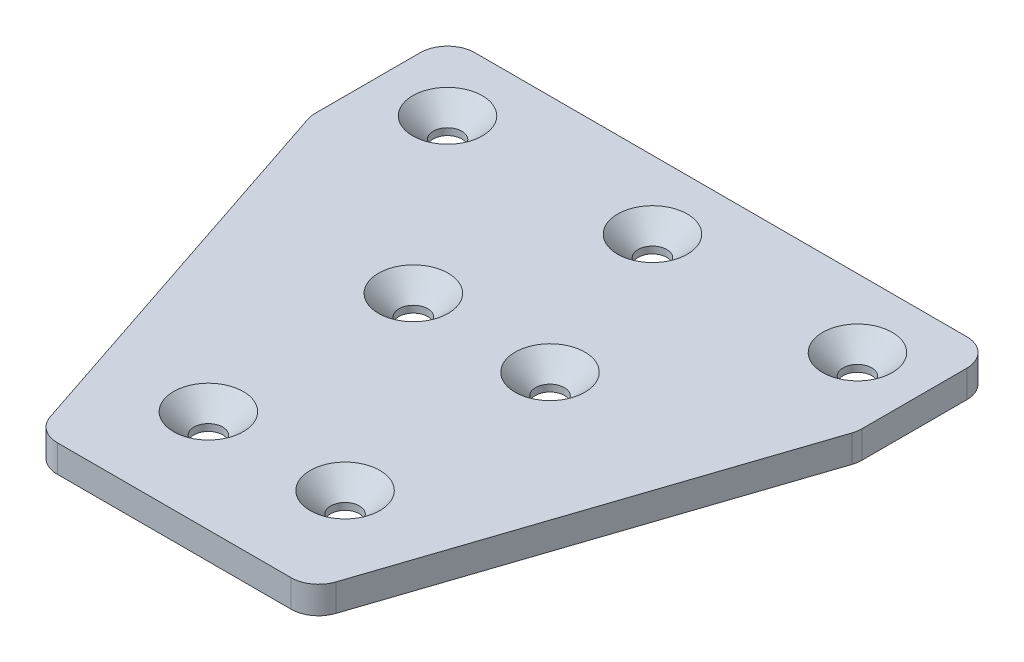
SolidWorks part; units mm, degrees
ref_plane "Front Plane" through (0, 0, 0) normal (0, 0, 1) x (1, 0, 0)
ref_plane "Top Plane" through (0, 0, 0) normal (0, 1, 0) x (1, 0, 0)
ref_plane "Right Plane" through (0, 0, 0) normal (1, 0, 0) x (0, 0, -1)
sketch "Sketch1" plane through (0, 0, 0) normal (0, 1, 0) x (1, 0, 0)
  line L0 (0, -40) -> (0, 0) construction
  line L1 (-40, -10) -> (40, -10)
  line L2 (-40, -10) -> (-40, 10)
  line L3 (-40, 10) -> (40, 10)
  line L4 (40, -10) -> (40, 10)
  line L5 (-40, -10) -> (40, 10) construction
  line L6 (-40, 10) -> (40, -10) construction
  line L7 (-20, -70) -> (20, -70)
  line L8 (-20, -70) -> (-20, -10)
  line L9 (-20, -10) -> (20, -10)
  line L10 (20, -70) -> (20, -10)
  line L11 (-20, -70) -> (20, -10) construction
  line L12 (-20, -10) -> (20, -70) construction
  line L13 (-40, -10) -> (-20, -70)
  line L14 (20, -70) -> (40, -10)
  line L15 (-40, 10) -> (-20, -10) construction
  line L16 (-20, -10) -> (-20, 10) construction
  line L17 (-20, 10) -> (-40, -10) construction
  line L18 (40, 10) -> (20, -10) construction
  line L19 (-10, -40) -> (-10, -25) construction
  line L20 (-10, -40) -> (-10, -55) construction
  line L21 (-10, -40) -> (0, -40) construction
  line L22 (0, -40) -> (10, -40) construction
  line L23 (10, -55) -> (10, -40) construction
  line L24 (10, -40) -> (10, -25) construction
  circle A0 centre (-30, 0) radius 2.1
  circle A1 centre (30, 0) radius 2.1
  circle A2 centre (0, 0) radius 2.1
  circle A3 centre (-10, -25) radius 2.1
  circle A4 centre (10, -25) radius 2.1
  circle A5 centre (10, -55) radius 2.1
  circle A6 centre (-10, -55) radius 2.1
  point P0 (0, 0)
  point P6 (0, -40)
  dimension "D6" = 4.2
  dimension "D1" = 60
  dimension "D2" = 40
  dimension "D3" = 20
  dimension "D4" = 80
  dimension "D5" = 45
  dimension "D7" = 10
extrude "Boss-Extrude1" add sketch "Sketch1" along normal blind 4 contours L7 L10 L1 L8 A6 A5 A4 A3 | L1 L13 L8 | L10 L14 L1 | L1 L4 L3 L2 A2 A1 A0
chamfer "Chamfer1" distance 3 angle 45 7 edges at (10, 4, 57.1) (-10, 4, 57.1) (10, 4, 27.1) (-10, 4, 27.1) (30, 4, 2.1) (0, 4, 2.1) (-30, 4, 2.1)
fillet "Fillet1" radius 4 6 edges at (-40, 2, 10) (-40, 2, -10) (40, 2, -10) (40, 2, 10) (20, 2, 70) (-20, 2, 70)
